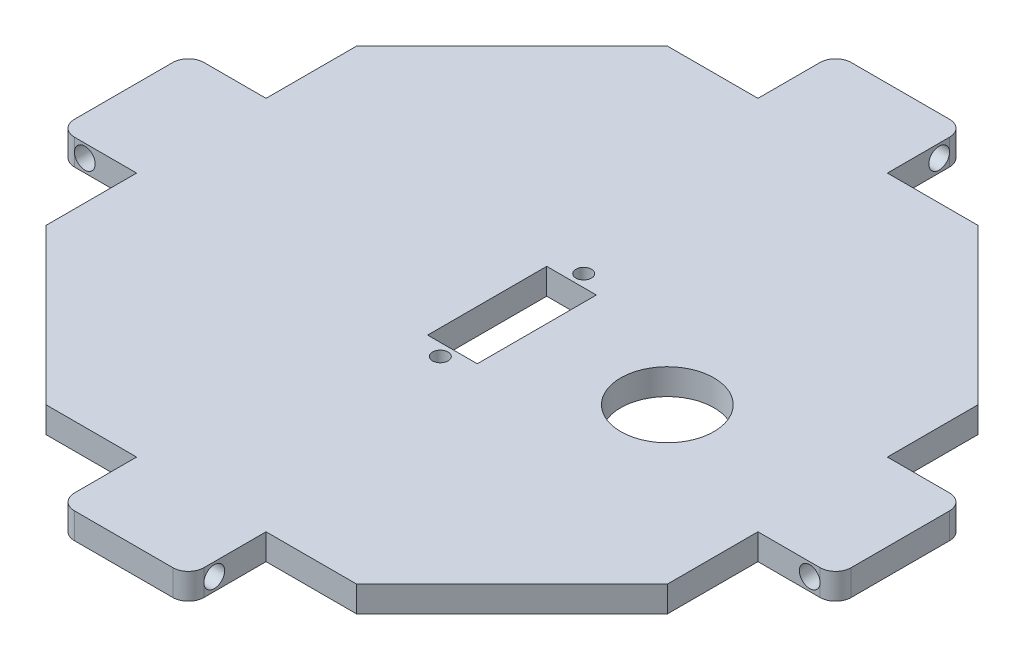
SolidWorks part; units mm, degrees
material "6061 합금"
ref_plane "정면" through (0, 0, 0) normal (0, 0, 1) x (1, 0, 0)
ref_plane "윗면" through (0, 0, 0) normal (0, 1, 0) x (1, 0, 0)
ref_plane "우측면" through (0, 0, 0) normal (1, 0, 0) x (0, 0, -1)
sketch "스케치1" plane through (0, 0, 0) normal (0, 1, 0) x (1, 0, 0)
  line L7 (39, 0) -> (-66.3, 0) construction
  line L9 (0, 39) -> (0, -39) construction
  line L14 (-30, -60) -> (30, -60)
  line L15 (30, -60) -> (60, -30)
  line L16 (60, -30) -> (60, 30)
  line L17 (60, 30) -> (30, 60)
  line L18 (30, 60) -> (-30, 60)
  line L19 (-30, 60) -> (-60, 30)
  line L20 (-60, 30) -> (-60, -30)
  line L21 (-60, -30) -> (-30, -60)
  line L22 (-60, 12.5) -> (-75, 12.5)
  line L23 (-75, 12.5) -> (-75, -12.5)
  line L24 (-75, -12.5) -> (-60, -12.5)
  line L25 (-12.5, -60) -> (-12.5, -75)
  line L26 (-12.5, -75) -> (12.5, -75)
  line L27 (12.5, -75) -> (12.5, -60)
  line L28 (60, -12.5) -> (75, -12.5)
  line L29 (75, -12.5) -> (75, 12.5)
  line L30 (75, 12.5) -> (60, 12.5)
  line L31 (-12.5, 60) -> (-12.5, 75)
  line L32 (-12.5, 75) -> (12.5, 75)
  line L33 (12.5, 75) -> (12.5, 60)
  point P0 (0, 0)
  dimension "D3" = 60
  dimension "D4" = 60
  dimension "D5" = 60
  dimension "D6" = 60
  dimension "D7" = 30
  dimension "D8" = 30
  dimension "D9" = 30
  dimension "D10" = 30
  dimension "D11" = 30
  dimension "D12" = 30
  dimension "D13" = 30
  dimension "D15" = 25
  dimension "D16" = 25
  dimension "D17" = 25
  dimension "D18" = 25
  dimension "D19" = 15
  dimension "D21" = 15
  dimension "D22" = 15
  dimension "D23" = 15
  dimension "D24" = 12.5
  dimension "D25" = 12.5
  dimension "D26" = 12.5
extrude "보스-돌출1" add sketch "스케치1" along normal blind 5
fillet "필렛1" radius 3 8 edges at (-12.5, 2.5, 75) (75, 2.5, 12.5) (75, 2.5, -12.5) (12.5, 2.5, -75) (-12.5, 2.5, -75) (-75, 2.5, -12.5) (-75, 2.5, 12.5) (12.5, 2.5, 75)
sketch "스케치11" plane through (0, 0, 12.5) normal (0, 0, 1) x (1, 0, 0)
  line L0 (-75, 0) -> (-75, 5) construction
  line L1 (-72, 5) -> (-60, 5) construction
  line L2 (75, 5) -> (75, 0) construction
  line L3 (60, 5) -> (72, 5) construction
  circle A0 centre (-70, 2.5) radius 2
  circle A1 centre (70, 2.5) radius 2
  dimension "D1" = 4
  dimension "D6" = 4
  dimension "D2" = 5
  dimension "D3" = 2.5
  dimension "D4" = 5
  dimension "D5" = 2.5
extrude "컷-돌출6" cut sketch "스케치11" against normal through all
sketch "스케치12" plane through (-12.5, 0, 0) normal (-1, 0, 0) x (0, 0, 1)
  line L0 (-75, 0) -> (-75, 5) construction
  line L1 (-60, 5) -> (-72, 5) construction
  line L2 (75, 5) -> (75, 0) construction
  circle A0 centre (-70, 2.5) radius 2
  circle A1 centre (70, 2.5) radius 2
  dimension "D3" = 4
  dimension "D4" = 4
  dimension "D1" = 5
  dimension "D2" = 2.5
  dimension "D5" = 5
extrude "컷-돌출7" cut sketch "스케치12" against normal through all
sketch "스케치13" plane through (0, 5, 0) normal (0, 1, 0) x (1, 0, 0)
  line L0 (-28.6523, 0) -> (16.6354, 0) construction
  line L1 (-4.7953, 11.5) -> (4.7953, 11.5)
  line L2 (-4.7953, 11.5) -> (-4.7953, -11.5)
  line L3 (-4.7953, -11.5) -> (4.7953, -11.5)
  line L4 (4.7953, 11.5) -> (4.7953, -11.5)
  line L5 (-4.7953, 11.5) -> (4.7953, -11.5) construction
  line L6 (-4.7953, -11.5) -> (4.7953, 11.5) construction
  circle A0 centre (0, 13.85) radius 1.5
  circle A1 centre (30, 0) radius 9
  circle A2 centre (0, -13.85) radius 1.5
  point P0 (0, 0)
  dimension "D1" = 23
  dimension "D2" = 18
  dimension "D4" = 3
  dimension "D3" = 13.85
extrude "컷-돌출8" cut sketch "스케치13" against normal blind 10
